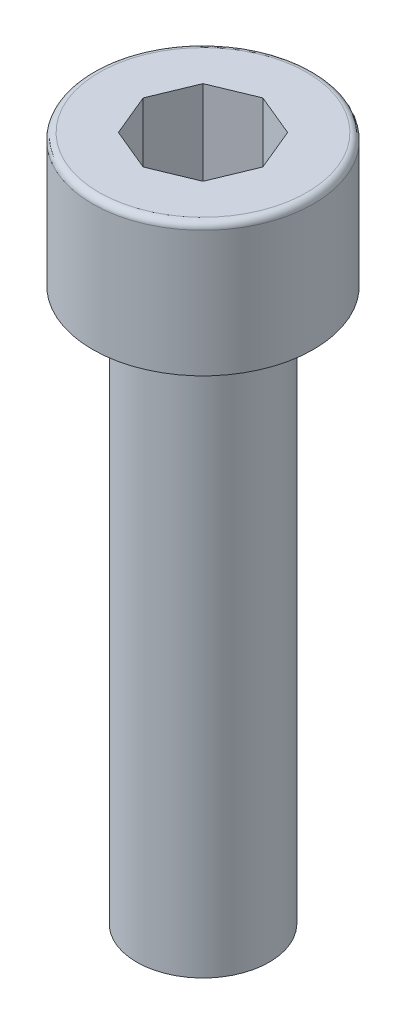
SolidWorks part; units mm, degrees
ref_plane "Front Plane" through (0, 0, 0) normal (0, 0, 1) x (1, 0, 0)
ref_plane "Top Plane" through (0, 0, 0) normal (0, 1, 0) x (1, 0, 0)
ref_plane "Right Plane" through (0, 0, 0) normal (1, 0, 0) x (0, 0, -1)
sketch "Sketch1" plane through (0, 0, 0) normal (0, 1, 0) x (1, 0, 0)
  circle A0 centre (0, 0) radius 3
  dimension "D1" = 6
extrude "Boss-Extrude1" add sketch "Sketch1" along normal blind 25
cosmetic thread "Cosmetic Thread1" parameters "D1"=23, "D2"=4.891
sketch "Sketch2" plane through (0, 25, 0) normal (0, 1, 0) x (1, 0, 0)
  line L1 (2.706, 0) -> (1.9134, 1.9134)
  line L2 (1.9134, 1.9134) -> (0, 2.706)
  line L3 (0, 2.706) -> (-1.9134, 1.9134)
  line L4 (-1.9134, 1.9134) -> (-2.706, 0)
  line L5 (-2.706, 0) -> (-1.9134, -1.9134)
  line L6 (-1.9134, -1.9134) -> (0, -2.706)
  line L7 (0, -2.706) -> (1.9134, -1.9134)
  line L8 (1.9134, -1.9134) -> (2.706, 0)
  circle A0 centre (0, 0) radius 5
  circle A1 centre (0, 0) radius 2.5 construction
  circle M1 centre (0, 0) radius 3
  dimension "D1" = 5
  dimension "D2" = 10
extrude "Boss-Extrude2" add sketch "Sketch2" along normal blind 6 contours A0 M1 | L8 L7 L6 L5 L4 L3 L2 L1 M1
fillet "Fillet1" radius 0.3 1 edges at (0, 31, 5)
fillet "Fillet2" radius 0.25 1 edges at (0, 25, 3)
